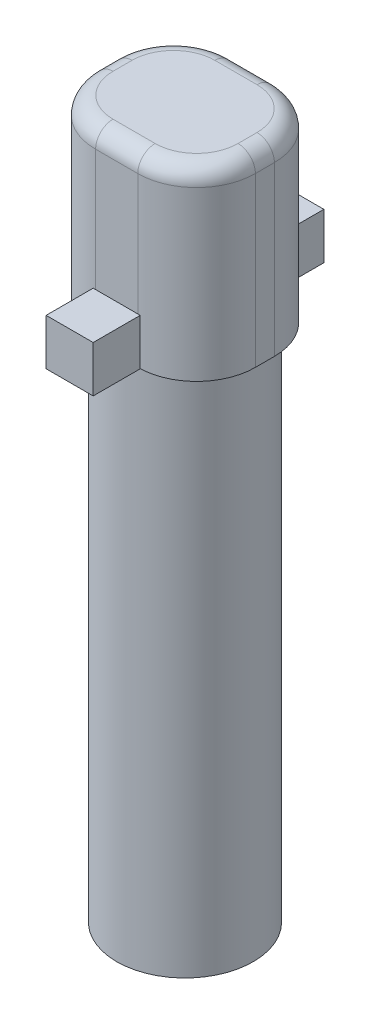
SolidWorks part; units mm, degrees
ref_plane "Front Plane" through (0, 0, 0) normal (0, 0, 1) x (1, 0, 0)
ref_plane "Top Plane" through (0, 0, 0) normal (0, 1, 0) x (1, 0, 0)
ref_plane "Right Plane" through (0, 0, 0) normal (1, 0, 0) x (0, 0, -1)
sketch "Sketch1" plane through (0, 0, 0) normal (0, 1, 0) x (1, 0, 0)
  circle A0 centre (0, 0) radius 2.95
  dimension "D1" = 5.9
extrude "Boss-Extrude1" add sketch "Sketch1" along normal blind 22.686 contours A0
sketch "Sketch2" plane through (0, 0, 0) normal (0, -1, 0) x (1, 0, 0)
  circle A1 centre (0, 0) radius 1.75
  dimension "D1" = 3.5
extrude "Cut-Extrude1" [suppressed] cut sketch "Sketch2" against normal blind 2.5
sketch "Sketch3" plane through (0, 22.686, 0) normal (0, 1, 0) x (1, 0, 0)
  line L1 (-3.45, 2.95) -> (3.45, 2.95)
  line L2 (-3.45, 2.95) -> (-3.45, -2.95)
  line L3 (-3.45, -2.95) -> (3.45, -2.95)
  line L4 (3.45, 2.95) -> (3.45, -2.95)
  line L5 (-3.45, 2.95) -> (3.45, -2.95) construction
  line L6 (-3.45, -2.95) -> (3.45, 2.95) construction
  point P0 (0, 0)
  dimension "D1" = 6.9
  dimension "D2" = 5.9
extrude "Boss-Extrude2" add sketch "Sketch3" along normal blind 8
fillet "Fillet1" radius 2.54 4 edges at (-3.45, 26.686, -2.95) (3.45, 26.686, -2.95) (3.45, 26.686, 2.95) (-3.45, 26.686, 2.95)
fillet "Fillet2" radius 0.75 8 edges at (3.45, 30.686, 0) (2.7061, 30.686, 2.2061) (2.7061, 30.686, -2.2061) (0, 30.686, -2.95) (-2.7061, 30.686, -2.2061) (-3.45, 30.686, 0) (-2.7061, 30.686, 2.2061) (0, 30.686, 2.95)
sketch "Sketch4" plane through (0, 30.686, 0) normal (0, 1, 0) x (1, 0, 0)
  line L0 (0, 2.95) -> (0, -2.95) construction
  line L1 (-0.91, 2.95) -> (0.91, 2.95) construction
  line L2 (0.91, -2.95) -> (-0.91, -2.95) construction
  line L3 (-1.016, 2.95) -> (-1.016, 4.982)
  line L4 (-1.016, 4.982) -> (1.016, 4.982)
  line L5 (1.016, 4.982) -> (1.016, 2.95)
  line L6 (1.016, 2.95) -> (-1.016, 2.95)
  line L7 (0, 4.982) -> (0, 2.95) construction
  line L8 (-3.45, 0) -> (3.45, 0) construction
  line L9 (-3.45, -0.41) -> (-3.45, 0.41) construction
  line L10 (3.45, 0.41) -> (3.45, -0.41) construction
  line L11 (0, -4.982) -> (0, -2.95) construction
  line L12 (1.016, -2.95) -> (-1.016, -2.95)
  line L13 (1.016, -4.982) -> (1.016, -2.95)
  line L14 (-1.016, -4.982) -> (1.016, -4.982)
  line L15 (-1.016, -2.95) -> (-1.016, -4.982)
  dimension "D1" = 2.032
  dimension "D2" = 2.032
extrude "Boss-Extrude3" add sketch "Sketch4" along normal blind 2 from surface at -8 starting at face at (2.1204, 22.686, 0)
